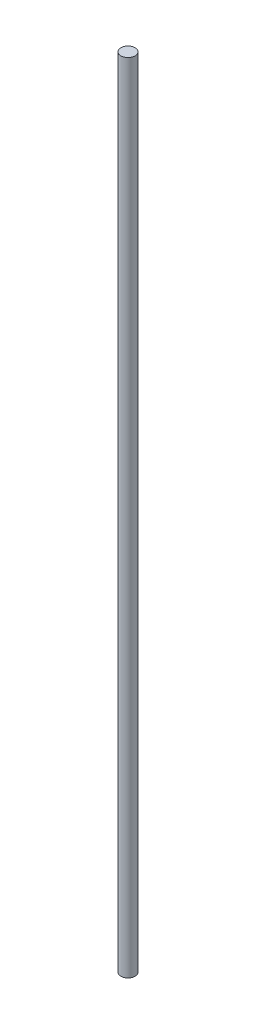
SolidWorks part; units mm, degrees
material "Plain Carbon Steel"
ref_plane "Front Plane" through (0, 0, 0) normal (0, 0, 1) x (1, 0, 0)
ref_plane "Top Plane" through (0, 0, 0) normal (0, 1, 0) x (1, 0, 0)
ref_plane "Right Plane" through (0, 0, 0) normal (1, 0, 0) x (0, 0, -1)
sketch "Sketch1" plane through (0, 0, 0) normal (0, 0, 1) x (1, 0, 0)
  line L1 (0, 0) -> (4, 0)
  line L2 (0, 0) -> (0, 450)
  line L3 (0, 450) -> (4, 450)
  line L4 (4, 0) -> (4, 450)
  dimension "D1" = 4
  dimension "D2" = 450
revolve "Revolve1" add sketch "Sketch1" angle 360 about L2
